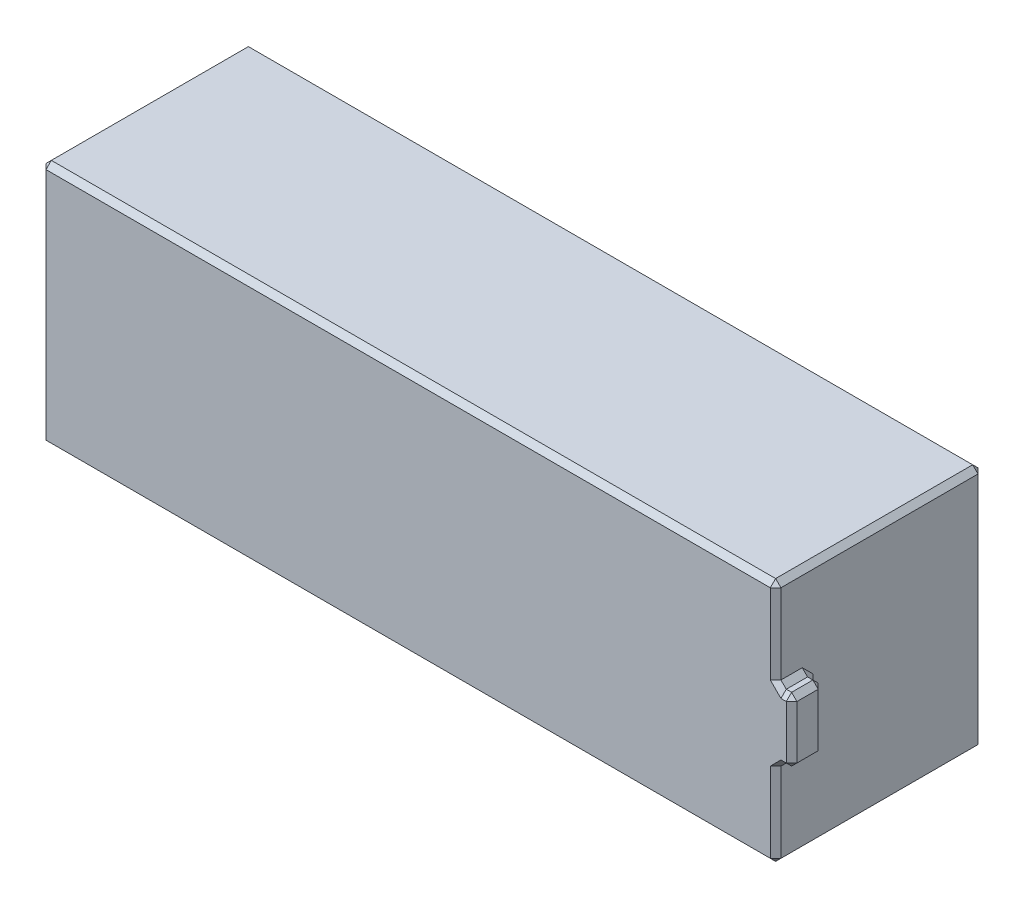
SolidWorks part; units mm, degrees
ref_plane "Front Plane" through (0, 0, 0) normal (0, 0, 1) x (1, 0, 0)
ref_plane "Top Plane" through (0, 0, 0) normal (0, 1, 0) x (1, 0, 0)
ref_plane "Right Plane" through (0, 0, 0) normal (1, 0, 0) x (0, 0, -1)
sketch "Sketch1" plane through (0, 0, 0) normal (0, 0, 1) x (1, 0, 0)
  line L1 (-69, 23) -> (69, 23)
  line L2 (-69, 23) -> (-69, -23)
  line L3 (-69, -23) -> (69, -23)
  line L4 (69, 23) -> (69, -23)
  line L5 (-69, 23) -> (69, -23) construction
  line L6 (-69, -23) -> (69, 23) construction
  point P0 (0, 0)
  dimension "D1" = 138
  dimension "D2" = 46
extrude "Boss-Extrude1" add sketch "Sketch1" along normal mid plane 39
sketch "Sketch2" plane through (69, 0, 0) normal (1, 0, 0) x (0, 0, -1)
  line L0 (0, 0) -> (-19.5, 0) construction
  line L1 (-19.5, -23) -> (-19.5, 23) construction
  line L3 (-13.5, 6) -> (-19.5, 6)
  line L4 (-13.5, 6) -> (-13.5, -6)
  line L5 (-13.5, -6) -> (-19.5, -6)
  line L6 (-19.5, 6) -> (-19.5, -6)
  line L7 (-13.5, 6) -> (-19.5, -6) construction
  line L8 (-13.5, -6) -> (-19.5, 6) construction
  point P5 (-16.5, 0)
  dimension "D1" = 12
  dimension "D2" = 6
extrude "Boss-Extrude2" add sketch "Sketch2" along normal mid plane 6
chamfer "Chamfer1" distance 1 angle 45 24 edges at (69, 0, 13.5) (69, 23, 0) (-69, 23, 0) (-69, -23, 0) (0, -23, -19.5) (-69, 0, -19.5) (0, 23, -19.5) (69, 0, -19.5) (69, -23, 0) (0, -23, 19.5) (-69, 0, 19.5) (0, 23, 19.5) (69, -14.5, 19.5) (69, 14.5, 19.5) (69, -6, 16.5) (69, 6, 16.5) (70.5, -6, 19.5) (70.5, -6, 13.5) (70.5, 6, 13.5) (70.5, 6, 19.5) (72, 6, 16.5) (72, 0, 13.5) (72, -6, 16.5) (72, 0, 19.5)
